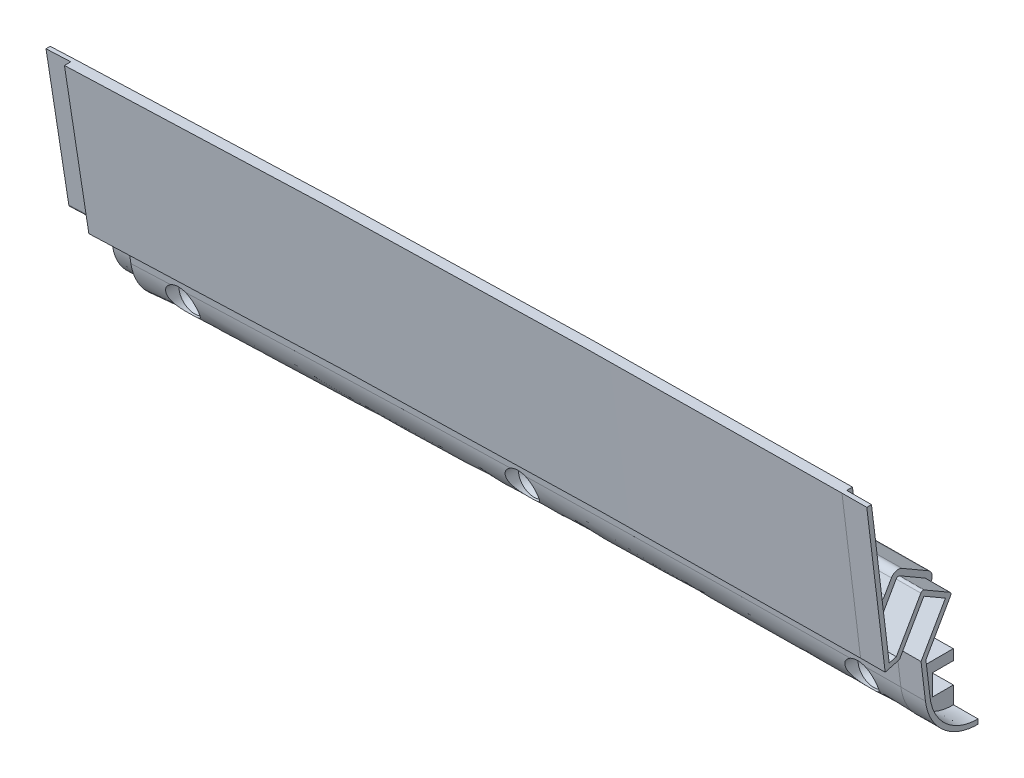
SolidWorks part; units mm, degrees
ref_plane "Front Plane" through (0, 0, 0) normal (0, 0, 1) x (1, 0, 0)
ref_plane "Top Plane" through (0, 0, 0) normal (0, 1, 0) x (1, 0, 0)
ref_plane "Right Plane" through (0, 0, 0) normal (1, 0, 0) x (0, 0, -1)
ref_plane "Plane3" through (-117.056, -3.871, 0) normal (0.9995, 0.0331, 0) x (0, 0, -1)
sketch "Sketch2" plane through (-117.056, -3.871, 0) normal (0.9995, 0.0331, 0) x (0, 0, -1)
  line L0 (-101.6, -41.1511) -> (-101.6, -45.9265)
  line L1 (-101.6, -41.1511) -> (-101.6, -45.9265)
  line L2 (-106.68, -45.9265) -> (-106.68, -50.6257)
  line L3 (-106.68, -45.9265) -> (-106.68, -50.6257)
  line L4 (-101.6, -50.6257) -> (-106.68, -50.6257)
  line L5 (-101.6, -50.6257) -> (-106.68, -50.6257)
  line L6 (-101.6, -50.6257) -> (-101.6, -56.1377)
  line L7 (-101.6, -50.6257) -> (-101.6, -56.1377)
  line L8 (-106.68, -45.9265) -> (-101.6, -45.9265)
  line L9 (-106.68, -45.9265) -> (-101.6, -45.9265)
  line L10 (-106.8705, -50.8162) -> (-108.9961, -53.9781) construction
  line L11 (-101.7905, -43.196) -> (-101.7905, -45.736)
  line L12 (-106.8705, -45.736) -> (-101.7905, -45.736)
  line L13 (-106.8705, -45.736) -> (-106.8705, -50.8162)
  line L14 (-101.7905, -50.8162) -> (-106.8705, -50.8162)
  line L15 (-101.7905, -50.8162) -> (-101.7905, -56.1377)
  line L16 (-101.7905, -43.196) -> (-101.6, -43.196)
  line L17 (-101.7905, -41.1511) -> (-101.7905, -45.736) construction
  line L18 (-120.8053, -33.0481) -> (-115.57, -36.0708)
  line L19 (-120.8053, -33.0481) -> (-115.57, -36.0708)
  line L20 (-109.601, -25.7318) -> (-114.8363, -22.709)
  line L21 (-109.601, -25.7318) -> (-114.8363, -22.709)
  line L22 (-114.8363, -22.709) -> (-120.8053, -33.0481)
  line L23 (-114.8363, -22.709) -> (-120.8053, -33.0481)
  line L24 (-115.57, -36.0708) -> (-109.601, -25.7318)
  line L25 (-115.57, -36.0708) -> (-109.601, -25.7318)
  line L26 (-115.57, -36.0708) -> (-114.523, -44.9291)
  line L28 (-118.1876, -34.5595) -> (-112.2186, -24.2204) construction
  line L29 (-114.6403, -39.5406) -> (-107.0838, -26.4518)
  line L30 (-107.7811, -23.8496) -> (-114.1162, -20.1918)
  line L31 (-116.7185, -20.8891) -> (-124.2749, -33.9778)
  line L33 (-106.1314, -24.8021) -> (-115.766, -19.2393) construction
  line L34 (-115.766, -19.2393) -> (-124.2749, -33.9778) construction
  line L35 (-114.6403, -39.5406) -> (-106.1314, -24.8021) construction
  line L36 (-124.2749, -33.9778) -> (-114.6403, -39.5406) construction
  line L37 (-112.9486, -36.6103) -> (-112.1701, -43.196)
  line L38 (-124.2749, -33.9778) -> (-128.0422, -2.1051)
  line L39 (-128.0422, -2.1051) -> (-132.6063, -0.4439)
  line L40 (-50.8, 0.7495) -> (-2184.4, 0.7495)
  line L41 (-125.822, 0.7495) -> (-133.442, 0.7495)
  line L42 (-122.1519, -30.3004) -> (-125.822, 0.7495)
  arc A0 (-114.523, -44.9291) -> (-101.7905, -56.1377) centre (-101.9108, -43.4383) ccw
  arc A2 (-114.1162, -20.1918) -> (-116.7185, -20.8891) centre (-115.0687, -21.8416) ccw
  arc A3 (-107.0838, -26.4518) -> (-107.7811, -23.8496) centre (-108.7336, -25.4993) ccw
  arc A4 (-133.442, 0.7495) -> (-132.6063, -0.4439) centre (-132.172, 0.7495) ccw
  point P41 (-133.442, 0.7495)
  dimension "D2" = 25.4
  dimension "D6" = 1.905
  dimension "D8" = 2.54
  dimension "D4" = 2.54
  dimension "D5" = 2.54
  dimension "D7" = 2.54
  dimension "D9" = 2.54
  dimension "D10" = 20
  dimension "D11" = 7.62
  dimension "D12" = 3.81
  dimension "D3" = 0.1905
sketch "Sketch3" plane through (0, 0, 101.6) normal (0, 0, 1) x (1, 0, 0)
  arc A0 (622.1039, -83.1998) -> (-622.1039, -83.1998) centre (0, -4954.4862) ccw construction
  arc A1 (622.1039, -83.1998) -> (-622.1039, -83.1998) centre (0, -4954.4862) ccw
sketch "Sketch4" plane through (-117.3306, 4.4304, 1117.6) normal (0.9995, 0.0331, 0) x (0, 0, -1)
  line L29 (1009.8189, -32.1556) -> (1003.4838, -28.4978) construction
  line L32 (1000.8815, -29.1951) -> (993.3251, -42.2838) construction
  line L35 (993.3251, -42.2838) -> (989.5578, -10.4111) construction
  line L50 (995.4481, -38.6064) -> (991.778, -7.5565) construction
  line L51 (1002.03, -44.3768) -> (1003.077, -53.235) construction
  line L52 (1015.8095, -59.1222) -> (1015.8095, -64.4437) construction
  line L53 (1015.8095, -59.1222) -> (1010.7295, -59.1222) construction
  line L54 (1010.7295, -54.042) -> (1010.7295, -59.1222) construction
  line L55 (1010.7295, -54.042) -> (1015.8095, -54.042) construction
  line L56 (1015.8095, -51.502) -> (1015.8095, -54.042) construction
  line L57 (1015.8095, -51.502) -> (1016, -51.502) construction
  line L58 (1004.6514, -44.9163) -> (1005.4299, -51.502) construction
  line L60 (1002.7637, -31.015) -> (996.7947, -41.3541) construction
  line L61 (1007.999, -34.0377) -> (1002.7637, -31.015) construction
  line L62 (1002.03, -44.3768) -> (1007.999, -34.0377) construction
  line L64 (991.5295, -5.4538) -> (988.9718, -5.4538)
  line L69 (1009.8189, -32.1556) -> (1003.4838, -28.4978)
  line L70 (1000.8815, -29.1951) -> (999.2724, -31.9822)
  line L71 (993.3251, -42.2838) -> (988.9718, -5.4538)
  line L74 (994.5502, -31.0104) -> (991.5295, -5.4538)
  line L75 (1002.03, -44.3768) -> (1003.077, -53.235)
  line L76 (1015.8095, -59.1222) -> (1015.8095, -64.4437)
  line L77 (1015.8095, -59.1222) -> (1010.7295, -59.1222)
  line L78 (1010.7295, -54.042) -> (1010.7295, -59.1222)
  line L79 (1010.7295, -54.042) -> (1015.8095, -54.042)
  line L80 (1015.8095, -51.502) -> (1015.8095, -54.042)
  line L81 (1015.8095, -51.502) -> (1007.6873, -51.502)
  line L82 (1004.7505, -45.7539) -> (1005.1649, -49.2601)
  line L84 (1002.7637, -31.015) -> (996.7947, -41.3541)
  line L85 (1007.999, -34.0377) -> (1002.7637, -31.015)
  line L86 (1002.03, -44.3768) -> (1007.999, -34.0377)
  line L87 (996.7947, -41.3541) -> (993.3251, -42.2838)
  line L88 (1005.0732, -44.1858) -> (1010.5162, -34.7578)
  arc A8 (1010.5162, -34.7578) -> (1009.8189, -32.1556) centre (1008.8664, -33.8053) ccw construction
  arc A9 (1003.4838, -28.4978) -> (1000.8815, -29.1951) centre (1002.5313, -30.1476) ccw construction
  arc A11 (1003.077, -53.235) -> (1015.8095, -64.4437) centre (1015.6892, -51.7443) ccw construction
  arc A12 (1010.5162, -34.7578) -> (1009.8189, -32.1556) centre (1008.8664, -33.8053) ccw
  arc A13 (1003.4838, -28.4978) -> (1000.8815, -29.1951) centre (1002.5313, -30.1476) ccw
  arc A15 (1003.077, -53.235) -> (1015.8095, -64.4437) centre (1015.6892, -51.7443) ccw
  arc A16 (1005.1649, -49.2601) -> (1007.6873, -51.502) centre (1007.6873, -48.962) ccw
  arc A17 (1004.7505, -45.7539) -> (1005.0732, -44.1858) centre (1007.2729, -45.4558) cw
  arc A18 (994.5502, -31.0104) -> (999.2724, -31.9822) centre (997.0727, -30.7122) ccw
  dimension "D2" = 2.54
  dimension "D1" = 36.83
sweep "Sweep3" add profiles "Sketch4" path "Sketch3"
sketch "Sketch5" plane through (0, 0, 101.7905) normal (0, 0, -1) x (-1, 0, 0)
  line L0 (211.6509, -4.1577) -> (0, -4954.4862) construction
  line L1 (0, -4954.4862) -> (22.6652, -1.2703) construction
  line L2 (117.0808, -1.0187) -> (0, -4954.4862) construction
  arc A1 (628.0925, -39.606) -> (-627.2635, -39.5001) centre (0, -4954.4862) ccw construction
  point P16 (117.0808, -1.0187)
ref_plane "Plane1" through (-211.4422, -9.0402, 0) normal (-0.9991, -0.0427, 0) x (0.0427, -0.9991, 0)
ref_plane "Plane2" through (-22.6706, -0.1037, 0) normal (1, 0.0046, 0) x (-0.0046, 1, 0)
other "SurfaceCut1"
other "SurfaceCut2"
sketch "Sketch8" plane through (-117.056, -3.871, 0) normal (0.9995, 0.0331, 0) x (0, 0, -1)
  line L0 (-106.8705, -50.8162) -> (-106.8705, -45.736)
  line L1 (-106.8705, -50.8162) -> (-106.8705, -45.736)
  line L2 (-106.8705, -48.2761) -> (-119.5705, -48.2761)
  line L3 (-119.5705, -48.2761) -> (-119.5705, -44.4661)
  line L4 (-119.5705, -44.4661) -> (-110.6805, -44.4661)
  line L5 (-110.6805, -44.4661) -> (-108.7755, -46.3711)
  line L6 (-108.7755, -46.3711) -> (-106.8705, -46.3711)
  line L7 (-119.5705, -48.2761) -> (-117.7248, -48.2761) construction
  dimension "D1" = 1.905
  dimension "D2" = 1.905
  dimension "D3" = 12.7
  dimension "D4" = 45
  dimension "D5" = 3.81
revolve "Cut-Revolve1" cut sketch "Sketch8" angle 360 about L7
sketch "Sketch9" plane through (0, 0, 106.8705) normal (0, 0, -1) x (-1, 0, 0)
  line L0 (198.0737, -52.2212) -> (197.8686, -57.297) construction
  line L1 (32.934, -48.3318) -> (32.8999, -53.4117) construction
  arc A1 (209.5755, -52.6994) -> (22.4502, -48.2726) centre (0, -4954.4862) ccw construction
  arc A2 (209.3585, -57.7748) -> (22.4269, -53.3526) centre (0, -4954.4862) ccw construction
  point P8 (197.9712, -54.7591)
  point P11 (0, -4954.4862)
  point P16 (115.4604, -52.1207)
  dimension "D1" = 82.55
  dimension "D2" = 82.55
sketch "Sketch10" plane through (0, 0, 106.8705) normal (0, 0, -1) x (-1, 0, 0)
  line L0 (32.934, -48.3318) -> (32.8999, -53.4117) construction
  point P0 (32.917, -50.8717)
  point P1 (197.9712, -54.7591)
pattern_sketch "Sketch-Pattern1" of "Cut-Revolve1" driven by "Sketch10"
sketch "Sketch12" plane through (0, 0, 101.7905) normal (0, 0, -1) x (-1, 0, 0)
  line L0 (22.4618, -45.7328) -> (0, -4954.4862) construction
  line L1 (0, -4954.4862) -> (16.4928, -45.7091) construction
  arc A1 (209.684, -50.1619) -> (22.4618, -45.7328) centre (0, -4954.4862) ccw construction
  arc A2 (22.4618, -45.7328) -> (16.4928, -45.7091) centre (0, -4954.4862) ccw
  dimension "D1" = 5.969
sketch "Sketch11" plane through (-22.6706, -0.1037, 0) normal (1, 0.0046, 0) x (0, 0, -1)
  line L0 (-127.4772, 0.4166) -> (-123.2949, -34.9658)
  line L1 (-123.2949, -34.9658) -> (-121.5584, -34.5006)
  line L2 (-121.5584, -34.5006) -> (-115.5722, -24.132)
  line L3 (-114.7047, -23.8996) -> (-108.5896, -27.4302)
  line L4 (-108.3571, -28.2976) -> (-114.3903, -38.7475)
  line L5 (-114.3903, -38.7475) -> (-113.3879, -47.2283)
  line L6 (-127.4931, 0.5508) -> (-123.2949, -34.9658) construction
  line L7 (-101.7905, -58.5707) -> (-101.7905, -57.4277)
  line L8 (-101.7905, -53.2494) -> (-101.7905, -58.5707) construction
  line L9 (-101.7905, -57.4277) -> (-101.8013, -57.4277)
  line L10 (-115.2547, -23.5821) -> (-108.0396, -27.7477) construction
  line L11 (-108.0396, -27.7477) -> (-114.3903, -38.7475) construction
  line L12 (-121.5584, -34.5006) -> (-115.2547, -23.5821) construction
  line L18 (-126.0705, 0.4166) -> (-128.6282, 0.4166)
  line L19 (-128.6282, 0.4166) -> (-124.2749, -36.4117)
  line L20 (-124.2749, -36.4117) -> (-120.8053, -35.4821)
  line L21 (-120.8053, -35.4821) -> (-114.8363, -25.1435)
  line L22 (-114.8363, -25.1435) -> (-109.601, -28.1661)
  line L23 (-109.601, -28.1661) -> (-115.57, -38.5047)
  line L24 (-115.57, -38.5047) -> (-114.523, -47.3625)
  line L25 (-101.7905, -58.5707) -> (-101.7905, -53.2494)
  line L26 (-101.7905, -53.2494) -> (-106.8705, -53.2494)
  line L27 (-106.8705, -53.2494) -> (-106.8705, -48.1694)
  line L28 (-106.8705, -48.1694) -> (-101.7905, -48.1694)
  line L29 (-101.7905, -48.1694) -> (-101.7905, -45.6295)
  line L30 (-101.7905, -45.6295) -> (-109.9127, -45.6295)
  line L31 (-112.4351, -43.3877) -> (-112.8495, -39.8818)
  line L32 (-112.5268, -38.3137) -> (-107.0838, -28.8861)
  line L33 (-107.781, -26.284) -> (-114.1162, -22.6264)
  line L34 (-116.7185, -23.3237) -> (-118.3276, -26.1106)
  line L35 (-123.0498, -25.1389) -> (-126.0705, 0.4166)
  line L36 (-127.4772, 0.4166) -> (-128.6282, 0.4166)
  line L37 (-128.6282, 0.4166) -> (-124.2749, -36.4117)
  line L38 (-124.2749, -36.4117) -> (-120.8053, -35.4821)
  line L39 (-120.8053, -35.4821) -> (-114.8363, -25.1435)
  line L40 (-114.8363, -25.1435) -> (-109.601, -28.1661)
  line L41 (-109.601, -28.1661) -> (-115.57, -38.5047)
  line L42 (-115.57, -38.5047) -> (-114.523, -47.3625)
  arc A0 (-108.5896, -27.4302) -> (-108.3571, -28.2976) centre (-108.9071, -27.9801) cw
  arc A1 (-115.5722, -24.132) -> (-114.7047, -23.8996) centre (-115.0222, -24.4495) cw
  arc A4 (-112.4351, -43.3877) -> (-109.9127, -45.6295) centre (-109.9127, -43.0896) ccw
  arc A5 (-112.5268, -38.3137) -> (-112.8495, -39.8818) centre (-110.3273, -39.5836) ccw
  arc A6 (-107.0838, -28.8861) -> (-107.781, -26.284) centre (-108.7335, -27.9337) ccw
  arc A7 (-114.1162, -22.6264) -> (-116.7185, -23.3237) centre (-115.0687, -24.2762) ccw
  spline S0 degree 1 poles (-113.3879, -47.2283) (-101.8013, -57.4277) knots 0 0 1 1 construction
  spline S1 degree 3 poles (-113.3879, -47.2283) (-113.3048, -47.9312) (-113.0054, -49.3311) (-111.9316, -51.9219) (-109.7159, -54.7453) (-106.0351, -56.9462) (-103.2019, -57.441) (-101.8013, -57.4277) knots 0 0 0 0 0.125 0.25 0.5 0.75 1 1 1 1
  spline S2 degree 3 poles (1806.7112, 500.6593) (415.3182, 185.4237) (-128.7728, 19.3055) (-114.2511, -48.8979) (-114.1523, -49.2753) (-113.8076, -50.3831) (-113.513, -51.0943) (-112.7943, -52.462) (-112.3662, -53.122) (-111.4114, -54.3345) (-110.8822, -54.8938) (-110.0099, -55.6614) (-109.7043, -55.9064) (-109.0766, -56.3638) (-108.7542, -56.5768) (-107.762, -57.1694) (-107.0674, -57.5033) (-105.9744, -57.9099) (-105.6018, -58.0293) (-104.8546, -58.2314) (-104.4782, -58.315) (-51.6561, -67.5542) (53.4105, 250.9973) (369.459, 1883.4824) knots -11.048432 -11.048432 -11.048432 -11.048432 0.0625 0.0625 0.125 0.125 0.25 0.25 0.375 0.375 0.5 0.5 0.5625 0.5625 0.625 0.625 0.75 0.75 0.8125 0.8125 0.875 0.875 9.519326 9.519326 9.519326 9.519326 only from (-114.523, -47.3625) to (-101.7905, -58.5707)
  spline S3 degree 3 poles (-966.8365, -555.2861) (-146.5253, 43.3444) (-110.7563, -19.4508) (-119.0219, -26.9033) (-119.2485, -27.051) (-119.7291, -27.2663) (-119.9898, -27.337) (-120.3827, -27.3799) (-120.5144, -27.384) (-120.779, -27.3716) (-120.9121, -27.3548) (-121.1705, -27.3014) (-121.297, -27.2648) (-121.5443, -27.1719) (-121.6661, -27.1149) (-121.896, -26.9844) (-122.0051, -26.9107) (-122.2115, -26.7465) (-122.3097, -26.6551) (-122.5785, -26.3621) (-122.7254, -26.141) (-131.5662, -6.8587) (104.7841, 84.3424) (817.0786, 315.6789) knots -5.03449 -5.03449 -5.03449 -5.03449 0.125 0.125 0.25 0.25 0.375 0.375 0.4375 0.4375 0.5 0.5 0.5625 0.5625 0.625 0.625 0.6875 0.6875 0.75 0.75 0.875 0.875 10.718854 10.718854 10.718854 10.718854 only from (-118.3276, -26.1106) to (-123.0498, -25.1389)
  spline S4 degree 3 poles (-114.523, -47.3625) (-114.4771, -47.7503) (-114.4136, -48.1349) (-114.2511, -48.8979) (-114.1523, -49.2753) (-113.8076, -50.3831) (-113.513, -51.0943) (-112.7943, -52.462) (-112.3662, -53.122) (-111.4114, -54.3345) (-110.8822, -54.8938) (-110.0099, -55.6614) (-109.7043, -55.9064) (-109.0766, -56.3638) (-108.7542, -56.5768) (-107.762, -57.1694) (-107.0674, -57.5033) (-105.9744, -57.9099) (-105.6018, -58.0293) (-104.8546, -58.2314) (-104.4782, -58.315) (-103.3407, -58.514) (-102.5713, -58.5781) (-101.7905, -58.5707) knots 0 0 0 0 0.0625 0.0625 0.125 0.125 0.25 0.25 0.375 0.375 0.5 0.5 0.5625 0.5625 0.625 0.625 0.75 0.75 0.8125 0.8125 0.875 0.875 1 1 1 1
  dimension "D3" = 0.635
  dimension "D1" = 0
  dimension "D2" = 1.143
sweep "Sweep4" add profiles "Sketch11" path "Sketch12"
sketch "Sketch14" plane through (-211.4422, -9.0402, 0) normal (-0.9991, -0.0427, 0) x (0, 0, 1)
  line L0 (113.0095, -42.7133) -> (113.9971, -34.3581)
  line L1 (113.9971, -34.3581) -> (107.5192, -23.138)
  line L2 (107.5192, -23.138) -> (115.3941, -18.5914)
  line L3 (115.3941, -18.5914) -> (121.8095, -29.7031)
  line L4 (121.8095, -29.7031) -> (122.9682, -30.0136)
  line L5 (122.9682, -30.0136) -> (127.1147, 5.0658)
  line L18 (128.6282, 4.8869) -> (126.0705, 4.8869)
  line L19 (126.0705, 4.8869) -> (123.0498, -20.6686)
  line L20 (118.3276, -21.6403) -> (116.7185, -18.8534)
  line L21 (114.1162, -18.1561) -> (107.7811, -21.8137)
  line L22 (107.0838, -24.4158) -> (112.5268, -33.8434)
  line L23 (112.8495, -35.4115) -> (112.4351, -38.9175)
  line L24 (109.9127, -41.1592) -> (101.7905, -41.1592)
  line L25 (101.7905, -41.1592) -> (101.7905, -43.6991)
  line L26 (101.7905, -43.6991) -> (106.8705, -43.6991)
  line L27 (106.8705, -43.6991) -> (106.8705, -48.7791)
  line L28 (106.8705, -48.7791) -> (101.7905, -48.7791)
  line L29 (101.7905, -48.7791) -> (101.7905, -54.1004)
  line L30 (114.523, -42.8922) -> (115.57, -34.0344)
  line L31 (115.57, -34.0344) -> (109.601, -23.6958)
  line L32 (109.601, -23.6958) -> (114.8363, -20.6732)
  line L33 (114.8363, -20.6732) -> (120.8053, -31.0118)
  line L34 (120.8053, -31.0118) -> (124.2749, -31.9414)
  line L35 (124.2749, -31.9414) -> (128.6282, 4.8869)
  line L36 (128.6282, 4.8869) -> (126.0705, 4.8869)
  line L37 (126.0705, 4.8869) -> (123.0498, -20.6686)
  line L38 (118.3276, -21.6403) -> (116.7185, -18.8534)
  line L39 (114.1162, -18.1561) -> (107.7811, -21.8137)
  line L40 (107.0838, -24.4158) -> (112.5268, -33.8434)
  line L41 (112.8495, -35.4115) -> (112.4351, -38.9175)
  line L42 (109.9127, -41.1592) -> (101.7905, -41.1592)
  line L43 (101.7905, -41.1592) -> (101.7905, -43.6991)
  line L44 (101.7905, -43.6991) -> (106.8705, -43.6991)
  line L45 (106.8705, -43.6991) -> (106.8705, -48.7791)
  line L46 (106.8705, -48.7791) -> (101.7905, -48.7791)
  line L47 (101.7905, -48.7791) -> (101.7905, -54.1004)
  line L48 (114.523, -42.8922) -> (115.57, -34.0344)
  line L49 (115.57, -34.0344) -> (109.601, -23.6958)
  line L50 (109.601, -23.6958) -> (114.8363, -20.6732)
  line L51 (114.8363, -20.6732) -> (120.8053, -31.0118)
  line L52 (120.8053, -31.0118) -> (124.2749, -31.9414)
  line L53 (124.2749, -31.9414) -> (128.6282, 4.8869)
  arc A4 (116.7185, -18.8534) -> (114.1162, -18.1561) centre (115.0687, -19.8059) ccw
  arc A5 (107.7811, -21.8137) -> (107.0838, -24.4158) centre (108.7335, -23.4634) ccw
  arc A6 (112.8495, -35.4115) -> (112.5268, -33.8434) centre (110.3273, -35.1133) ccw
  arc A7 (109.9127, -41.1592) -> (112.4351, -38.9175) centre (109.9127, -38.6193) ccw
  arc A8 (116.7185, -18.8534) -> (114.1162, -18.1561) centre (115.0687, -19.8059) ccw
  arc A9 (107.7811, -21.8137) -> (107.0838, -24.4158) centre (108.7335, -23.4634) ccw
  arc A10 (112.8495, -35.4115) -> (112.5268, -33.8434) centre (110.3273, -35.1133) ccw
  arc A11 (109.9127, -41.1592) -> (112.4351, -38.9175) centre (109.9127, -38.6193) ccw
  spline S0 degree 1 poles (101.8049, -52.5765) (113.0095, -42.7133) knots 0 0 1 1 construction
  spline S1 degree 3 poles (101.8049, -52.5765) (102.4893, -52.583) (103.8689, -52.4674) (106.4858, -51.7551) (109.4658, -49.9761) (112.0284, -46.7154) (112.8505, -44.0584) (113.0095, -42.7133) knots 0 0 0 0 0.125 0.25 0.5 0.75 1 1 1 1
  spline S2 degree 3 poles (-1420.2451, -2589.1907) (7.5348, 76.4537) (129.3579, -7.252) (122.7249, -21.671) (122.575, -21.8961) (122.2185, -22.2837) (122.0069, -22.4517) (121.6628, -22.6462) (121.5435, -22.702) (121.2955, -22.795) (121.1665, -22.8321) (120.908, -22.8851) (120.7774, -22.9014) (120.5134, -22.9137) (120.3791, -22.9094) (120.1163, -22.8803) (119.987, -22.8557) (119.7325, -22.7864) (119.6063, -22.7412) (119.2436, -22.578) (119.0214, -22.433) (93.7379, 0.421) (581.1886, 448.0858) (2362.312, 1968.4478) knots -7.286241 -7.286241 -7.286241 -7.286241 0.125 0.125 0.25 0.25 0.375 0.375 0.4375 0.4375 0.5 0.5 0.5625 0.5625 0.625 0.625 0.6875 0.6875 0.75 0.75 0.875 0.875 16.766809 16.766809 16.766809 16.766809 only from (123.0498, -20.6686) to (118.3276, -21.6403)
  spline S3 degree 3 poles (-288.3388, 2916.9987) (-102.777, 757.3692) (19.5454, -60.9671) (103.3479, -54.0254) (103.7348, -53.9753) (104.8774, -53.7738) (105.6202, -53.5717) (107.068, -53.0324) (107.777, -52.6914) (109.1008, -51.8981) (109.7227, -51.4442) (110.5948, -50.6762) (110.8766, -50.4042) (111.4099, -49.8396) (111.662, -49.5468) (112.3757, -48.6378) (112.795, -47.9912) (113.3369, -46.9586) (113.5026, -46.6041) (113.7979, -45.8886) (113.9285, -45.5258) (132.5439, 14.5864) (-288.4354, 203.7302) (-2703.1014, 979.8882) knots -13.349036 -13.349036 -13.349036 -13.349036 0.0625 0.0625 0.125 0.125 0.25 0.25 0.375 0.375 0.5 0.5 0.5625 0.5625 0.625 0.625 0.75 0.75 0.8125 0.8125 0.875 0.875 11.030088 11.030088 11.030088 11.030088 only from (101.7905, -54.1004) to (114.523, -42.8922)
  spline S4 degree 3 poles (123.0498, -20.6686) (123.0184, -20.9338) (122.9449, -21.1927) (122.7249, -21.671) (122.575, -21.8961) (122.2185, -22.2837) (122.0069, -22.4517) (121.6628, -22.6462) (121.5435, -22.702) (121.2955, -22.795) (121.1665, -22.8321) (120.908, -22.8851) (120.7774, -22.9014) (120.5134, -22.9137) (120.3791, -22.9094) (120.1163, -22.8803) (119.987, -22.8557) (119.7325, -22.7864) (119.6063, -22.7412) (119.2436, -22.578) (119.0214, -22.433) (118.6267, -22.0763) (118.4611, -21.8716) (118.3276, -21.6403) knots 0 0 0 0 0.125 0.125 0.25 0.25 0.375 0.375 0.4375 0.4375 0.5 0.5 0.5625 0.5625 0.625 0.625 0.6875 0.6875 0.75 0.75 0.875 0.875 1 1 1 1
  spline S5 degree 3 poles (101.7905, -54.1004) (102.1809, -54.1041) (102.5705, -54.0898) (103.3479, -54.0254) (103.7348, -53.9753) (104.8774, -53.7738) (105.6202, -53.5717) (107.068, -53.0324) (107.777, -52.6914) (109.1008, -51.8981) (109.7227, -51.4442) (110.5948, -50.6762) (110.8766, -50.4042) (111.4099, -49.8396) (111.662, -49.5468) (112.3757, -48.6378) (112.795, -47.9912) (113.3369, -46.9586) (113.5026, -46.6041) (113.7979, -45.8886) (113.9285, -45.5258) (114.2702, -44.4227) (114.4313, -43.6677) (114.523, -42.8922) knots 0 0 0 0 0.0625 0.0625 0.125 0.125 0.25 0.25 0.375 0.375 0.5 0.5 0.5625 0.5625 0.625 0.625 0.75 0.75 0.8125 0.8125 0.875 0.875 1 1 1 1
  dimension "D1" = 0
  dimension "D2" = 1.524
sketch "Sketch15" plane through (-211.4422, -9.0402, 0) normal (-0.9991, -0.0427, 0) x (0, 0, 1)
  line L0 (113.0095, -42.7133) -> (113.9971, -34.3581) construction
  line L1 (113.9971, -34.3581) -> (107.5192, -23.138) construction
  line L2 (107.5192, -23.138) -> (115.3941, -18.5914) construction
  line L3 (115.3941, -18.5914) -> (121.8095, -29.7031) construction
  line L4 (121.8095, -29.7031) -> (122.9682, -30.0136) construction
  line L5 (122.9682, -30.0136) -> (127.1147, 5.0658) construction
  line L6 (113.0095, -42.7133) -> (113.9724, -34.5675)
  line L7 (113.8917, -34.1755) -> (107.5192, -23.138)
  line L8 (107.5192, -23.138) -> (115.3941, -18.5914)
  line L9 (115.3941, -18.5914) -> (121.678, -29.4753)
  line L10 (122.0636, -29.7712) -> (122.2594, -29.8237)
  line L11 (123.0543, -29.2848) -> (127.0936, 4.8869)
  line L12 (101.7905, -48.7791) -> (101.7905, -54.1004) construction
  line L13 (101.7905, -48.7791) -> (101.7905, -52.5765)
  line L14 (101.8049, -52.5765) -> (101.7905, -52.5765)
  line L18 (124.2749, -31.9414) -> (128.6282, 4.8869)
  line L19 (128.6282, 4.8869) -> (126.0705, 4.8869)
  line L20 (126.0705, 4.8869) -> (123.0498, -20.6686)
  line L21 (118.3276, -21.6403) -> (116.7185, -18.8534)
  line L22 (114.1162, -18.1561) -> (107.7811, -21.8137)
  line L23 (107.0838, -24.4158) -> (112.5268, -33.8434)
  line L24 (112.8495, -35.4115) -> (112.4351, -38.9175)
  line L25 (109.9127, -41.1592) -> (101.7905, -41.1592)
  line L26 (101.7905, -41.1592) -> (101.7905, -43.6991)
  line L27 (101.7905, -43.6991) -> (106.8705, -43.6991)
  line L28 (106.8705, -43.6991) -> (106.8705, -48.7791)
  line L29 (106.8705, -48.7791) -> (101.7905, -48.7791)
  line L30 (101.7905, -48.7791) -> (101.7905, -54.1004)
  line L31 (114.523, -42.8922) -> (115.57, -34.0344)
  line L32 (115.57, -34.0344) -> (109.601, -23.6958)
  line L33 (109.601, -23.6958) -> (114.8363, -20.6732)
  line L34 (114.8363, -20.6732) -> (120.8053, -31.0118)
  line L35 (120.8053, -31.0118) -> (124.2749, -31.9414)
  line L37 (127.0936, 4.8869) -> (126.0705, 4.8869)
  line L38 (126.0705, 4.8869) -> (123.0498, -20.6686)
  line L39 (118.3276, -21.6403) -> (116.7185, -18.8534)
  line L40 (114.1162, -18.1561) -> (107.7811, -21.8137)
  line L41 (107.0838, -24.4158) -> (112.5268, -33.8434)
  line L42 (112.8495, -35.4115) -> (112.4351, -38.9175)
  line L43 (109.9127, -41.1592) -> (101.7905, -41.1592)
  line L44 (101.7905, -41.1592) -> (101.7905, -43.6991)
  line L45 (101.7905, -43.6991) -> (106.8705, -43.6991)
  line L46 (106.8705, -43.6991) -> (106.8705, -48.7791)
  line L47 (106.8705, -48.7791) -> (101.7905, -48.7791)
  arc A0 (113.9724, -34.5675) -> (113.8917, -34.1755) centre (113.3418, -34.493) ccw
  arc A1 (121.678, -29.4753) -> (122.0636, -29.7712) centre (122.2279, -29.1578) ccw
  arc A2 (122.2594, -29.8237) -> (123.0543, -29.2848) centre (122.4237, -29.2103) ccw
  arc A4 (116.7185, -18.8534) -> (114.1162, -18.1561) centre (115.0687, -19.8059) ccw
  arc A5 (107.7811, -21.8137) -> (107.0838, -24.4158) centre (108.7335, -23.4634) ccw
  arc A6 (112.8495, -35.4115) -> (112.5268, -33.8434) centre (110.3273, -35.1133) ccw
  arc A7 (109.9127, -41.1592) -> (112.4351, -38.9175) centre (109.9127, -38.6193) ccw
  arc A8 (116.7185, -18.8534) -> (114.1162, -18.1561) centre (115.0687, -19.8059) ccw
  arc A9 (107.7811, -21.8137) -> (107.0838, -24.4158) centre (108.7335, -23.4634) ccw
  arc A10 (112.8495, -35.4115) -> (112.5268, -33.8434) centre (110.3273, -35.1133) ccw
  arc A11 (109.9127, -41.1592) -> (112.4351, -38.9175) centre (109.9127, -38.6193) ccw
  spline S0 degree 3 poles (1969.6766, 654.3437) (8.5109, 56.766) (75.3403, -60.2329) (106.4858, -51.7551) (109.4658, -49.9761) (134.2797, -18.4018) (-16.091, 107.1074) (-926.156, -1745.3361) knots -5.450838 -5.450838 -5.450838 -5.450838 0.125 0.25 0.5 0.75 7.512309 7.512309 7.512309 7.512309 only from (101.8049, -52.5765) to (113.0095, -42.7133) construction
  spline S1 degree 3 poles (101.8049, -52.5765) (102.4893, -52.583) (103.8689, -52.4674) (106.4858, -51.7551) (109.4658, -49.9761) (112.0284, -46.7154) (112.8505, -44.0584) (113.0095, -42.7133) knots 0 0 0 0 0.125 0.25 0.5 0.75 1 1 1 1
  spline S2 degree 3 poles (-1420.2451, -2589.1907) (7.5348, 76.4537) (129.3579, -7.252) (122.7249, -21.671) (122.575, -21.8961) (122.2185, -22.2837) (122.0069, -22.4517) (121.6628, -22.6462) (121.5435, -22.702) (121.2955, -22.795) (121.1665, -22.8321) (120.908, -22.8851) (120.7774, -22.9014) (120.5134, -22.9137) (120.3791, -22.9094) (120.1163, -22.8803) (119.987, -22.8557) (119.7325, -22.7864) (119.6063, -22.7412) (119.2436, -22.578) (119.0214, -22.433) (93.7379, 0.421) (581.1886, 448.0858) (2362.312, 1968.4478) knots -7.286241 -7.286241 -7.286241 -7.286241 0.125 0.125 0.25 0.25 0.375 0.375 0.4375 0.4375 0.5 0.5 0.5625 0.5625 0.625 0.625 0.6875 0.6875 0.75 0.75 0.875 0.875 16.766809 16.766809 16.766809 16.766809 only from (123.0498, -20.6686) to (118.3276, -21.6403)
  spline S3 degree 3 poles (-93.3253, 926.6784) (-10.5613, 232.0775) (53.1389, -58.1844) (103.3479, -54.0254) (103.7348, -53.9753) (104.8774, -53.7738) (105.6202, -53.5717) (107.068, -53.0324) (107.777, -52.6914) (109.1008, -51.8981) (109.7227, -51.4442) (110.5948, -50.6762) (110.8766, -50.4042) (111.4099, -49.8396) (111.662, -49.5468) (112.3757, -48.6378) (112.795, -47.9912) (113.3369, -46.9586) (113.5026, -46.6041) (113.7979, -45.8886) (113.9285, -45.5258) (125.9187, -6.8076) (-43.2917, 84.8615) (-804.6708, 350.8867) knots -7.947776 -7.947776 -7.947776 -7.947776 0.0625 0.0625 0.125 0.125 0.25 0.25 0.375 0.375 0.5 0.5 0.5625 0.5625 0.625 0.625 0.75 0.75 0.8125 0.8125 0.875 0.875 7.39364 7.39364 7.39364 7.39364 only from (101.7905, -54.1004) to (114.523, -42.8922)
  spline S4 degree 3 poles (123.0498, -20.6686) (123.0184, -20.9338) (122.9449, -21.1927) (122.7249, -21.671) (122.575, -21.8961) (122.2185, -22.2837) (122.0069, -22.4517) (121.6628, -22.6462) (121.5435, -22.702) (121.2955, -22.795) (121.1665, -22.8321) (120.908, -22.8851) (120.7774, -22.9014) (120.5134, -22.9137) (120.3791, -22.9094) (120.1163, -22.8803) (119.987, -22.8557) (119.7325, -22.7864) (119.6063, -22.7412) (119.2436, -22.578) (119.0214, -22.433) (118.6267, -22.0763) (118.4611, -21.8716) (118.3276, -21.6403) knots 0 0 0 0 0.125 0.125 0.25 0.25 0.375 0.375 0.4375 0.4375 0.5 0.5 0.5625 0.5625 0.625 0.625 0.6875 0.6875 0.75 0.75 0.875 0.875 1 1 1 1
  dimension "D2" = 0.635
  dimension "D1" = 0
sketch "Sketch16" plane through (0, 0, 101.7905) normal (0, 0, -1) x (-1, 0, 0)
  arc A0 (215.6474, -50.4205) -> (209.684, -50.1619) centre (0, -4954.4862) ccw
  arc A1 (209.684, -50.1619) -> (22.4618, -45.7328) centre (0, -4954.4862) ccw construction
  dimension "D1" = 5.969
sweep "Sweep5" add profiles "Sketch15" path "Sketch16"
